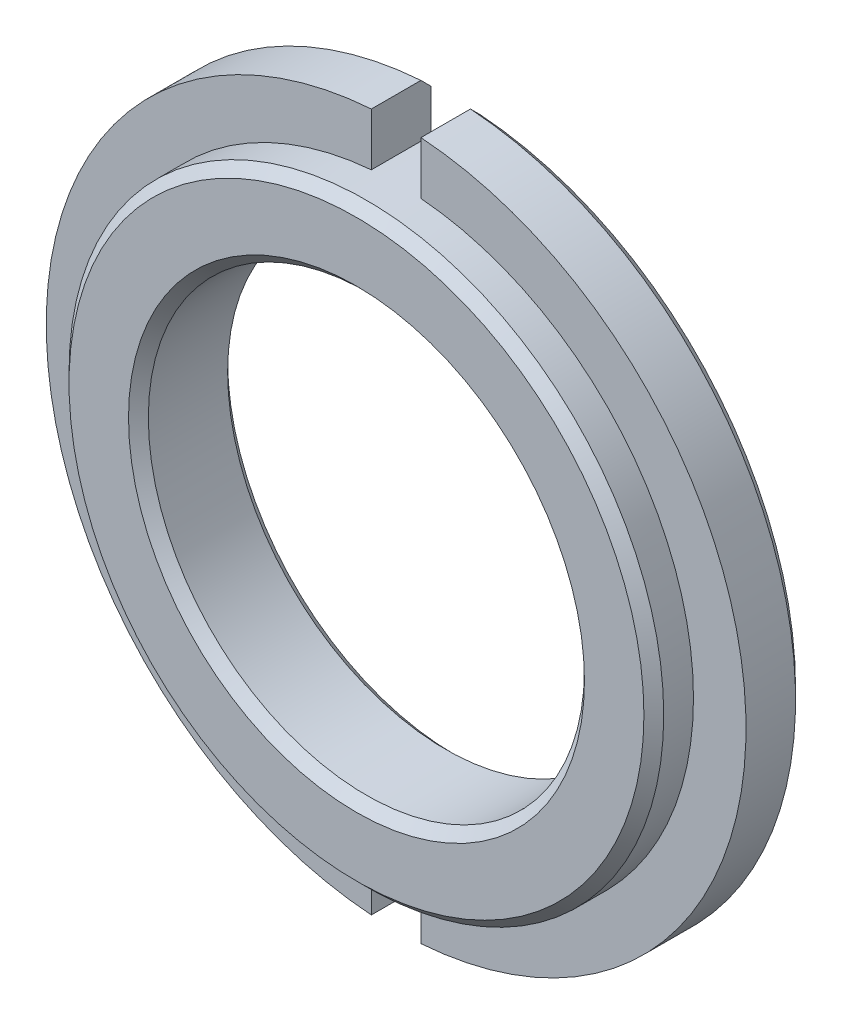
SolidWorks part; units mm, degrees
ref_plane "Front Plane" through (0, 0, 0) normal (0, 0, 1) x (1, 0, 0)
ref_plane "Top Plane" through (0, 0, 0) normal (0, 1, 0) x (1, 0, 0)
ref_plane "Right Plane" through (0, 0, 0) normal (1, 0, 0) x (0, 0, -1)
sketch "Sketch1" plane through (0, 0, 0) normal (0, 0, 1) x (1, 0, 0)
  circle A0 centre (0, 0) radius 17.65
  circle A1 centre (0, 0) radius 11
  dimension "D1" = 35.3
  dimension "D2" = 22
extrude "Boss-Extrude1" add sketch "Sketch1" along normal blind 5
sketch "Sketch2" plane through (0, 0, 5) normal (0, 0, 1) x (1, 0, 0)
  circle A0 centre (0, 0) radius 17.65
  circle A1 centre (0, 0) radius 15
  dimension "D1" = 30
extrude "Cut-Extrude1" cut sketch "Sketch2" against normal blind 2
sketch "Sketch3" plane through (0, 0, 3) normal (0, 0, 1) x (1, 0, 0)
  line L0 (0, 17.65) -> (0, -17.65) construction
  line L1 (1.25, 17.6057) -> (1.25, 14.9478)
  line L2 (-1.25, 17.6057) -> (-1.25, 14.9478)
  line L3 (1.25, -14.9478) -> (1.25, -17.6057)
  line L4 (-1.25, -14.9478) -> (-1.25, -17.6057)
  arc A0 (-1.25, -17.6057) -> (1.25, -17.6057) centre (0, 0) ccw
  arc A1 (-1.25, -14.9478) -> (1.25, -14.9478) centre (0, 0) ccw
  arc A2 (1.25, 14.9478) -> (-1.25, 14.9478) centre (0, 0) ccw
  arc A3 (1.25, 17.6057) -> (-1.25, 17.6057) centre (0, 0) ccw
  dimension "D1" = 1.25
extrude "Cut-Extrude3" cut sketch "Sketch3" against normal up to next
chamfer "Chamfer1" distance 0.5 angle 45 5 edges at (11, 0, 5) (15, 0, 5) (17.65, 0, 0) (-17.65, 0, 0) (11, 0, 0)
